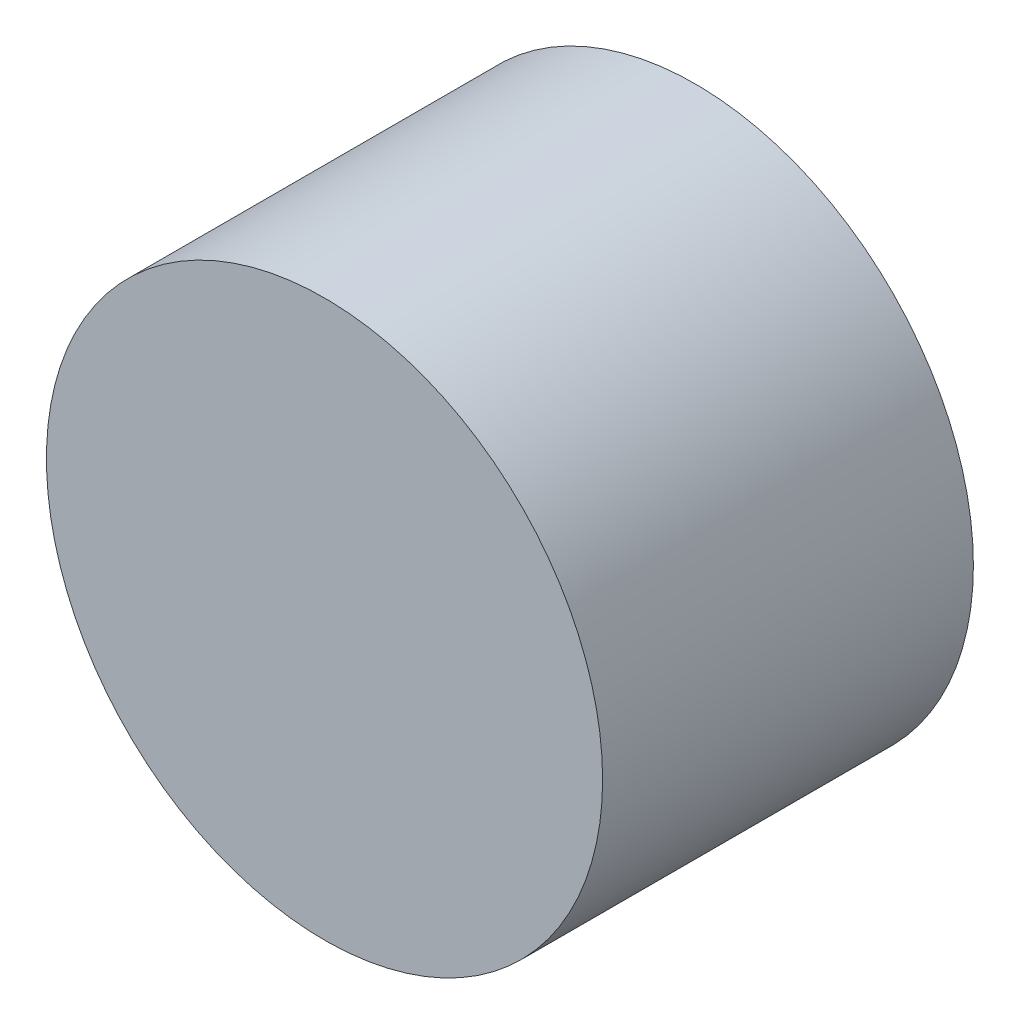
SolidWorks part; units mm, degrees
ref_plane "Plan de face" through (0, 0, 0) normal (0, 0, 1) x (1, 0, 0)
ref_plane "Plan de dessus" through (0, 0, 0) normal (0, 1, 0) x (1, 0, 0)
ref_plane "Plan de droite" through (0, 0, 0) normal (1, 0, 0) x (0, 0, -1)
sketch "Esquisse1" plane through (0, 0, 0) normal (0, 0, 1) x (1, 0, 0)
  circle A0 centre (0, 0) radius 75
  dimension "D1" = 150
extrude "Boss.-Extru.1" add sketch "Esquisse1" along normal blind 100
